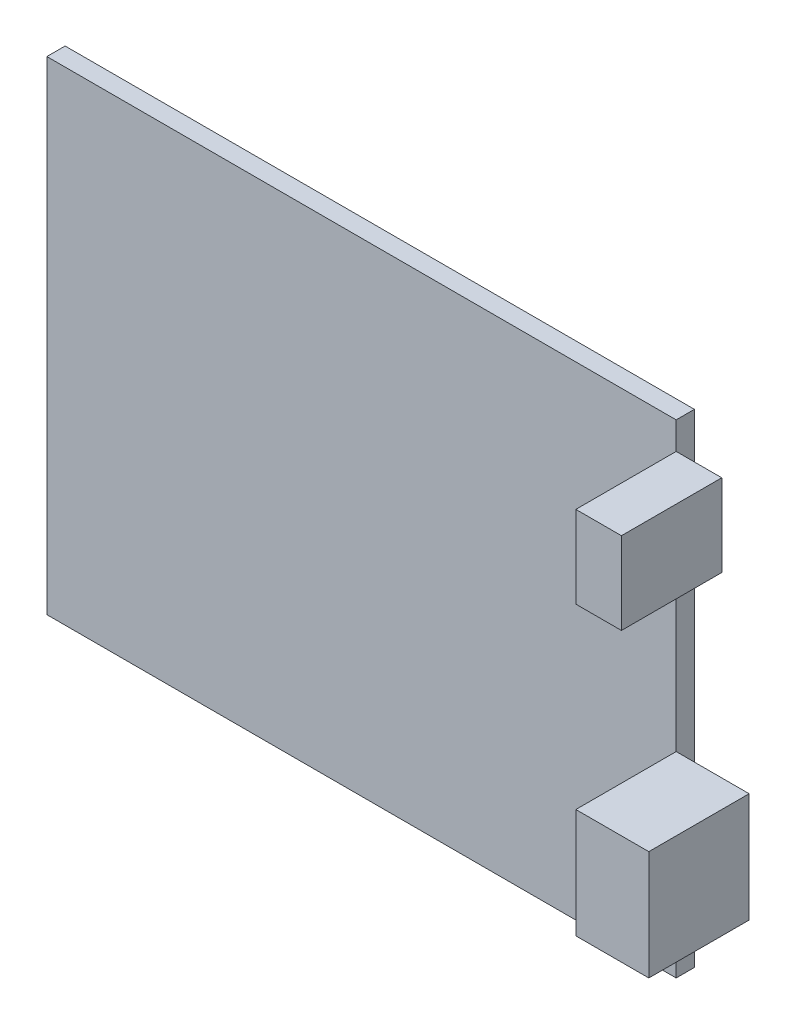
SolidWorks part; units mm, degrees
ref_plane "Plano frontal" through (0, 0, 0) normal (0, 0, 1) x (1, 0, 0)
ref_plane "Plano superior" through (0, 0, 0) normal (0, 1, 0) x (1, 0, 0)
ref_plane "Plano direito" through (0, 0, 0) normal (1, 0, 0) x (0, 0, -1)
sketch "Esboço1" plane through (0, 0, 0) normal (0, 0, 1) x (1, 0, 0)
  line L1 (0, 0) -> (69, 0)
  line L2 (0, 0) -> (0, 53)
  line L3 (0, 53) -> (69, 53)
  line L4 (69, 0) -> (69, 53)
  dimension "D1" = 69
  dimension "D2" = 53
extrude "Ressalto-extrusão1" add sketch "Esboço1" along normal blind 2
sketch "Esboço2" plane through (69, 0, 0) normal (1, 0, 0) x (0, 0, -1)
  line L0 (-2, 0) -> (-2, 53) construction
  line L1 (-2, 50) -> (-13, 50)
  line L2 (-2, 50) -> (-2, 41)
  line L3 (-2, 41) -> (-13, 41)
  line L4 (-13, 50) -> (-13, 41)
  line L5 (-2, 53) -> (0, 53) construction
  line L7 (-2, 21.5) -> (-13, 21.5)
  line L8 (-2, 21.5) -> (-2, 9.5)
  line L9 (-2, 9.5) -> (-13, 9.5)
  line L10 (-13, 21.5) -> (-13, 9.5)
  dimension "D1" = 11
  dimension "D2" = 9
  dimension "D3" = 3
  dimension "D4" = 40.5
  dimension "D5" = 11
  dimension "D6" = 12
extrude "Ressalto-extrusão2" add sketch "Esboço2" along normal blind 5 separate body
sketch "Esboço3" plane through (74, 0, 0) normal (1, 0, 0) x (0, 0, -1)
  line L4 (-2, 9.5) -> (-2, 21.5)
  line L5 (-2, 21.5) -> (-13, 21.5)
  line L6 (-13, 21.5) -> (-13, 9.5)
  line L7 (-13, 9.5) -> (-2, 9.5)
  line L8 (-2, 9.5) -> (-2, 21.5)
  line L9 (-2, 21.5) -> (-13, 21.5)
  line L10 (-13, 21.5) -> (-13, 9.5)
  line L11 (-13, 9.5) -> (-2, 9.5)
  dimension "D1" = 0
extrude "Ressalto-extrusão3" add sketch "Esboço3" along normal blind 3
